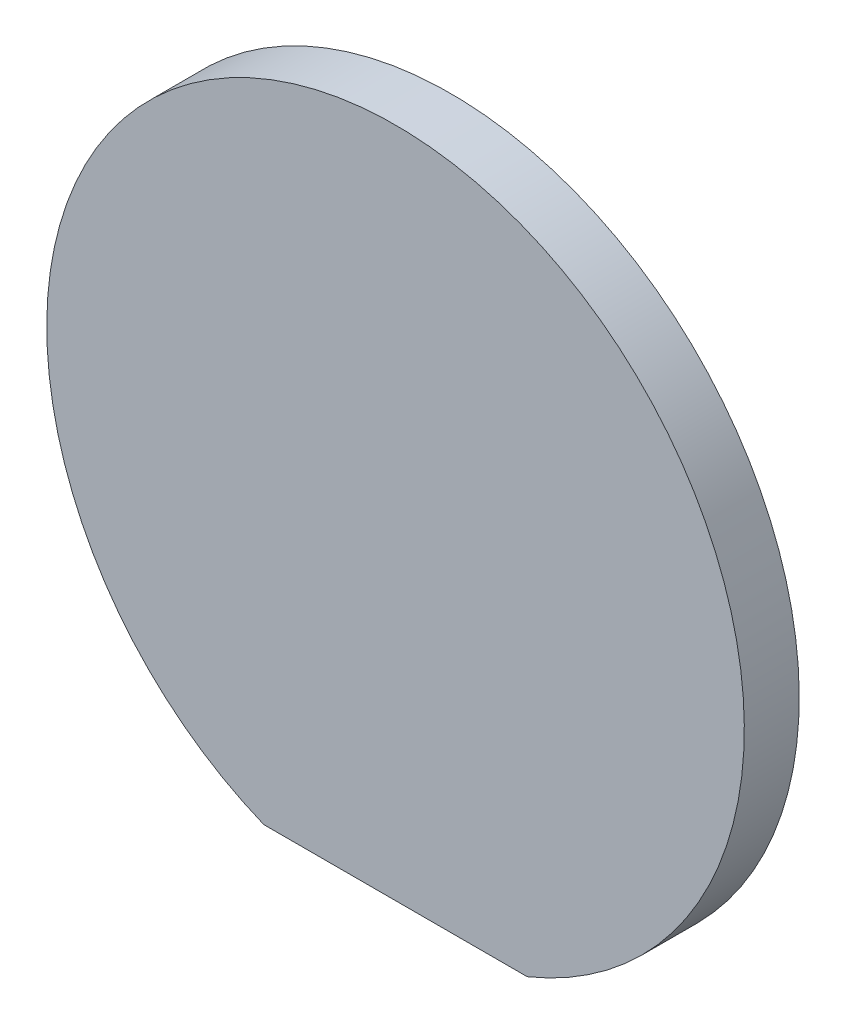
SolidWorks part; units mm, degrees
ref_plane "前视基准面" through (0, 0, 0) normal (0, 0, 1) x (1, 0, 0)
ref_plane "上视基准面" through (0, 0, 0) normal (0, 1, 0) x (1, 0, 0)
ref_plane "右视基准面" through (0, 0, 0) normal (1, 0, 0) x (0, 0, -1)
sketch "草图1" plane through (0, 0, 0) normal (0, 0, 1) x (1, 0, 0)
  circle A0 centre (0, 0) radius 6.35
  dimension "D1" = 12.7
extrude "凸台-拉伸1" add sketch "草图1" along normal blind 1
sketch "草图2" plane through (0, 0, 1) normal (0, 0, 1) x (1, 0, 0)
  line L0 (-5.8873, -5.88) -> (7.7033, -5.88)
  line L1 (-5.8873, -5.88) -> (-5.8873, -7.8058)
  line L2 (-5.8873, -7.8058) -> (7.7033, -7.8058)
  line L3 (7.7033, -7.8058) -> (7.7033, -5.88)
  dimension "D1" = 5.88
extrude "切除-拉伸1" cut sketch "草图2" against normal through all
